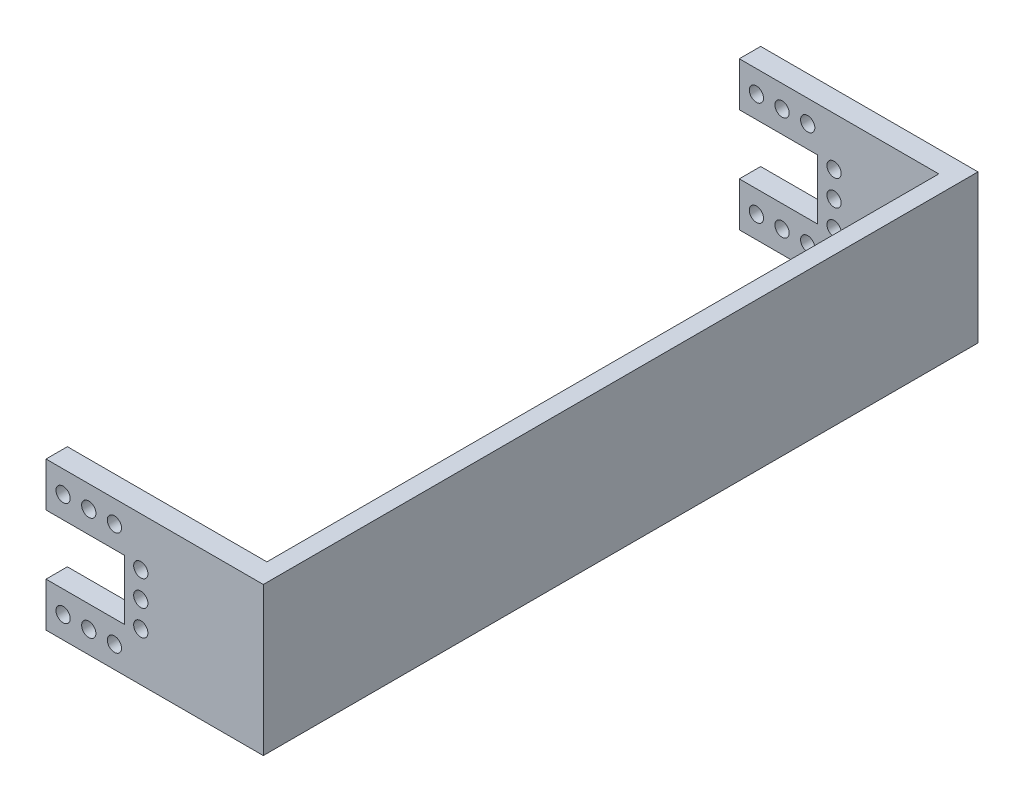
SolidWorks part; units mm, degrees
ref_plane "정면" through (0, 0, 0) normal (0, 0, 1) x (1, 0, 0)
ref_plane "윗면" through (0, 0, 0) normal (0, 1, 0) x (1, 0, 0)
ref_plane "우측면" through (0, 0, 0) normal (1, 0, 0) x (0, 0, -1)
sketch "스케치3" plane through (0, 0, -47.45) normal (0, 0, -1) x (-1, 0, 0)
  line L0 (0, 0) -> (-32.45, 0) construction
  line L2 (-4.45, -10.4) -> (-20.85, -10.4)
  line L4 (-4.45, 10.4) -> (-20.85, 10.4)
  line L8 (-4.45, 10.4) -> (-4.45, 4.2)
  line L9 (-4.45, -10.4) -> (-4.45, -4.2)
  line L10 (-4.45, 4.2) -> (-15.45, 4.2)
  line L11 (-4.45, -4.2) -> (-15.45, -4.2)
  line L12 (-15.45, 4.2) -> (-15.45, -4.2)
  line L13 (-20.85, 10.4) -> (-32.45, 10.4)
  line L14 (-20.85, -10.4) -> (-32.45, -10.4)
  line L15 (-32.45, 10.4) -> (-32.45, -10.4)
  point P3 (-10.45, 0)
  point P18 (-15.45, 0)
  circle M1 centre (-14.05, 7.3) radius 1
  circle M2 centre (-6.85, 7.3) radius 1
  circle M3 centre (-10.45, 7.3) radius 1
  circle M7 centre (-6.85, -7.3) radius 1
  circle M8 centre (-14.05, -7.3) radius 1
  circle M9 centre (-10.45, -7.3) radius 1
  circle M10 centre (-17.75, -3.6) radius 1
  circle M11 centre (-17.75, 3.6) radius 1
  circle M12 centre (-17.75, 0) radius 1
  circle M13 centre (-10.45, 0) radius 10.4
  dimension "D2" = 5
  dimension "D3" = 6.2
  dimension "D4" = 20.8
  dimension "D5" = 6
  dimension "D7" = 17
extrude "보스-돌출2" add sketch "스케치3" along normal blind 3 contours L0 L4 L13 L15 M13 | L0 L15 L14 L2 M13 | L0 L12 L10 L8 M13 M12 M2 M11 M3 M1 | L12 L0 L9 L11 M12 M13 M7 M9 M10 M8 | L8 L4 M13 | L2 L9 M13
ref_plane "평면2" through (0, 0, -0.3) normal (0, 0, -1) x (-1, 0, 0)
mirror "대칭 복사7" about plane through (0, 0, -0.3) normal (0, 0, -1) of bodies 103
sketch "스케치5" plane through (32.45, 0, 0) normal (1, 0, 0) x (0, 0, -1)
  line L1 (-49.85, 10.4) -> (50.45, 10.4)
  line L2 (-49.85, 10.4) -> (-49.85, -10.4)
  line L3 (-49.85, -10.4) -> (50.45, -10.4)
  line L4 (50.45, 10.4) -> (50.45, -10.4)
extrude "보스-돌출4" add sketch "스케치5" along normal blind 2.5
